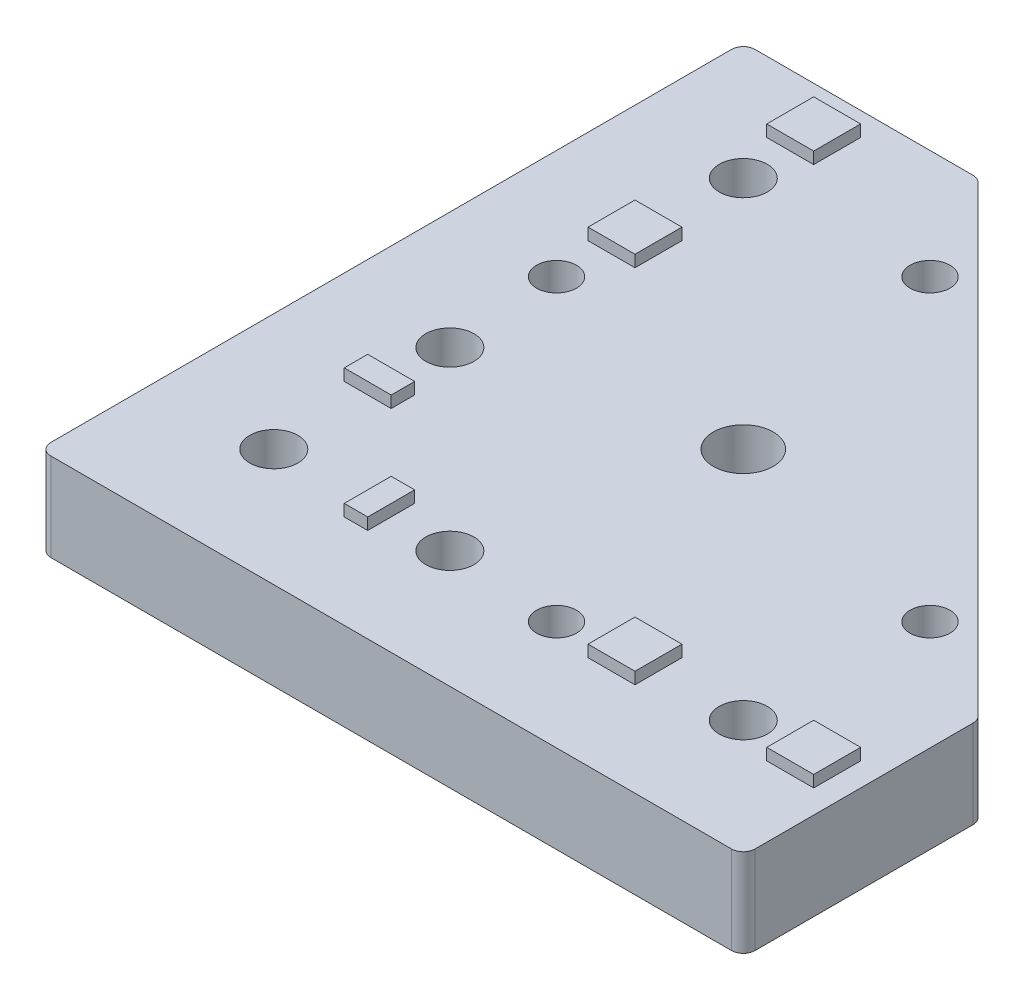
SolidWorks part; units mm, degrees
material "Алюминиевый сплав"
ref_plane "Спереди" through (0, 0, 0) normal (0, 0, 1) x (1, 0, 0)
ref_plane "Сверху" through (0, 0, 0) normal (0, 1, 0) x (1, 0, 0)
ref_plane "Справа" through (0, 0, 0) normal (1, 0, 0) x (0, 0, -1)
sketch "Эскиз1" plane through (0, 0, 0) normal (0, 1, 0) x (1, 0, 0)
  line L0 (0, 0) -> (0, 120)
  line L1 (0, 120) -> (40, 120)
  line L2 (40, 120) -> (120, 40)
  line L3 (120, 40) -> (120, 0)
  line L4 (120, 0) -> (0, 0)
  point P3 (1.2064, 0)
  dimension "D1" = 120
  dimension "D2" = 40
extrude "Бобышка-Вытянуть1" add sketch "Эскиз1" along normal blind 15
hole_wizard "Отверстие обработанное метчиком M121" positions "Эскиз2" profile "Эскиз3" tap size "M12" standard "ISO" end condition up to next
sketch "Эскиз2" plane through (0, 15, 0) normal (0, 1, 0) x (1, 0, 0)
  line L0 (0, 0) -> (120, 0) construction
  line L2 (120, 0) -> (120, 40) construction
  point P0 (60, 60)
  dimension "D1" = 60
  dimension "D2" = 60
sketch "Эскиз3" plane through (60, 15, -60) normal (1, 0, 0) x (0, 0, 1)
  line L0 (0, 0) -> (0, 15)
  line L1 (0, 15) -> (5.1, 15)
  line L2 (5.1, 15) -> (5.1, 0)
  line L5 (5.1, 0) -> (0, 0)
  line L11 (0, -6.35) -> (0, 107.95) construction
  dimension "Диаметр проходного сверла" = 10.2
  dimension "Глубина проходного сверла" = 15
cosmetic thread "Отверстие резьбы1" parameters "D2"=12
hole_wizard "Отверстие обработанное метчиком M81" positions "Эскиз4" profile "Эскиз5" tap size "M8" standard "ISO" end condition up to next
sketch "Эскиз4" plane through (0, 15, 0) normal (0, 1, 0) x (1, 0, 0)
  line L0 (50.4541, 101.3657) -> (18.6343, 69.5459)
  line L1 (18.6343, 69.5459) -> (69.5459, 18.6343)
  line L2 (69.5459, 18.6343) -> (101.3657, 50.4541)
  line L3 (101.3657, 50.4541) -> (50.4541, 101.3657)
  line L5 (120, 40) -> (40, 120) construction
  line L8 (50.4541, 101.3657) -> (69.5459, 18.6343)
  circle A0 centre (60, 60) radius 5.1
  circle A1 centre (60, 60) radius 5.1 construction
  point P0 (50.4541, 101.3657)
  point P2 (101.3657, 50.4541)
  point P4 (69.5459, 18.6343)
  point P6 (18.6343, 69.5459)
  point P41 (0, 0)
  dimension "D1" = 72
  dimension "D2" = 45
sketch "Эскиз5" plane through (50.4541, 15, -101.3657) normal (1, 0, 0) x (0, 0, 1)
  line L0 (0, 0) -> (0, 15)
  line L1 (0, 15) -> (3.4, 15)
  line L2 (3.4, 15) -> (3.4, 0)
  line L5 (3.4, 0) -> (0, 0)
  line L11 (0, -6.35) -> (0, 107.95) construction
  dimension "Диаметр проходного сверла" = 6.8
  dimension "Глубина проходного сверла" = 15
cosmetic thread "Отверстие резьбы2" parameters "D2"=8
cosmetic thread "Отверстие резьбы3" parameters "D2"=8
cosmetic thread "Отверстие резьбы4" parameters "D2"=8
cosmetic thread "Отверстие резьбы5" parameters "D2"=8
hole_wizard "Диаметр отверстия Ø8.2 (8.2)1" positions "Эскиз6" profile "Эскиз8" hole size "Ø8.2" standard "ISO" end condition up to next
sketch "Эскиз6" plane through (0, 15, 0) normal (0, 1, 0) x (1, 0, 0)
  line L0 (100, 20) -> (50, 20)
  line L1 (50, 20) -> (20, 20)
  line L2 (20, 20) -> (20, 50)
  line L3 (20, 50) -> (20, 100)
  line L5 (0, 0) -> (120, 0) construction
  line L6 (0, 120) -> (0, 0) construction
  point P0 (20, 100)
  point P2 (20, 50)
  point P4 (20, 20)
  point P6 (50, 20)
  point P8 (100, 20)
  dimension "D1" = 20
  dimension "D2" = 20
  dimension "D3" = 30
  dimension "D4" = 50
sketch "Эскиз8" plane through (20, 15, -100) normal (1, 0, 0) x (0, 0, 1)
  line L0 (0, 0) -> (0, 15)
  line L1 (0, 15) -> (4.1, 15)
  line L2 (4.1, 15) -> (4.1, 0)
  line L5 (4.1, 0) -> (0, 0)
  line L11 (0, -6.35) -> (0, 107.95) construction
  dimension "Диаметр сквозного отверстия" = 8.2
  dimension "Глубина сквозного отверстия" = 15
sketch "Эскиз9" plane through (0, 15, 0) normal (0, 1, 0) x (1, 0, 0)
  line L0 (0, 0) -> (80, 80) construction
  line L1 (16, 116) -> (24, 116)
  line L2 (16, 116) -> (16, 108)
  line L3 (16, 108) -> (24, 108)
  line L4 (24, 116) -> (24, 108)
  line L5 (16, 116) -> (24, 108) construction
  line L6 (16, 108) -> (24, 116) construction
  line L7 (16, 85.5459) -> (24, 85.5459)
  line L8 (16, 85.5459) -> (16, 77.5459)
  line L9 (16, 77.5459) -> (24, 77.5459)
  line L10 (24, 85.5459) -> (24, 77.5459)
  line L11 (16, 85.5459) -> (24, 77.5459) construction
  line L12 (16, 77.5459) -> (24, 85.5459) construction
  line L13 (16, 40) -> (24, 40)
  line L14 (16, 40) -> (16, 36)
  line L15 (16, 36) -> (24, 36)
  line L16 (24, 40) -> (24, 36)
  line L17 (16, 40) -> (24, 36) construction
  line L18 (16, 36) -> (24, 40) construction
  line L19 (120, 40) -> (40, 120) construction
  line L20 (20, 112) -> (20, 100) construction
  line L21 (20, 100) -> (20, 81.5459) construction
  line L22 (20, 81.5459) -> (20, 38) construction
  line L23 (81.5459, 20) -> (38, 20) construction
  line L24 (100, 20) -> (81.5459, 20) construction
  line L25 (112, 20) -> (100, 20) construction
  line L26 (36, 16) -> (40, 24) construction
  line L27 (40, 16) -> (36, 24) construction
  line L28 (77.5459, 16) -> (85.5459, 24) construction
  line L29 (85.5459, 16) -> (77.5459, 24) construction
  line L30 (108, 16) -> (116, 24) construction
  line L31 (116, 16) -> (108, 24) construction
  line L32 (40, 24) -> (36, 24)
  line L33 (36, 16) -> (36, 24)
  line L34 (40, 16) -> (36, 16)
  line L35 (40, 16) -> (40, 24)
  line L36 (85.5459, 24) -> (77.5459, 24)
  line L37 (77.5459, 16) -> (77.5459, 24)
  line L38 (85.5459, 16) -> (77.5459, 16)
  line L39 (85.5459, 16) -> (85.5459, 24)
  line L40 (116, 24) -> (108, 24)
  line L41 (108, 16) -> (108, 24)
  line L42 (116, 16) -> (108, 16)
  line L43 (116, 16) -> (116, 24)
  circle A0 centre (20, 100) radius 4.1 construction
  circle A1 centre (20, 50) radius 4.1 construction
  circle A2 centre (18.6343, 69.5459) radius 3.4 construction
  point P0 (20, 112)
  point P5 (20, 81.5459)
  point P10 (20, 38)
  point P23 (12, 80.1439)
  point P26 (12, 65.5613)
  point P31 (18, 33.6701)
  point P32 (18, 30.3688)
  point P51 (38, 20)
  point P52 (81.5459, 20)
  point P53 (112, 20)
  dimension "D5" = 12
  dimension "D1" = 8
  dimension "D2" = 12
  dimension "D3" = 12
  dimension "D4" = 4
extrude "Бобышка-Вытянуть2" add sketch "Эскиз9" along normal blind 2
fillet "Скругление1" radius 2 5 edges at (0, 7.5, -120) (0, 7.5, 0) (120, 7.5, 0) (120, 7.5, -40) (40, 7.5, -120)
